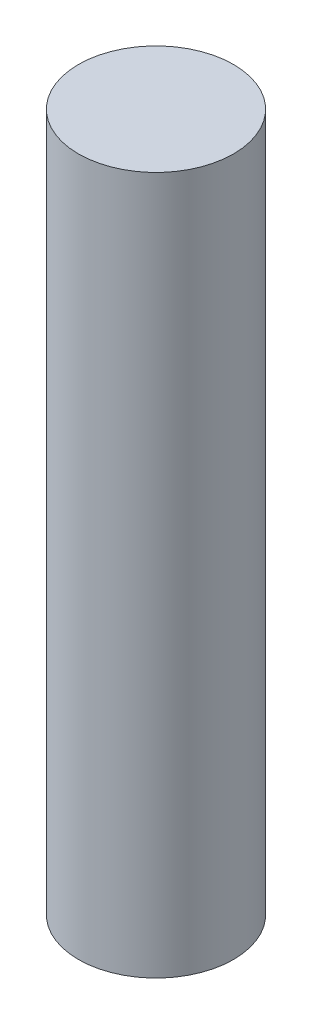
SolidWorks part; units mm, degrees
ref_plane "Front Plane" through (0, 0, 0) normal (0, 0, 1) x (1, 0, 0)
ref_plane "Top Plane" through (0, 0, 0) normal (0, 1, 0) x (1, 0, 0)
ref_plane "Right Plane" through (0, 0, 0) normal (1, 0, 0) x (0, 0, -1)
sketch "Axle Diameter" plane through (0, 0, 0) normal (0, 1, 0) x (1, 0, 0)
  circle A0 centre (0, 0) radius 12.7
  dimension "D1" = 25.4
extrude "Axle Extrude" add sketch "Axle Diameter" along normal blind 114.3
